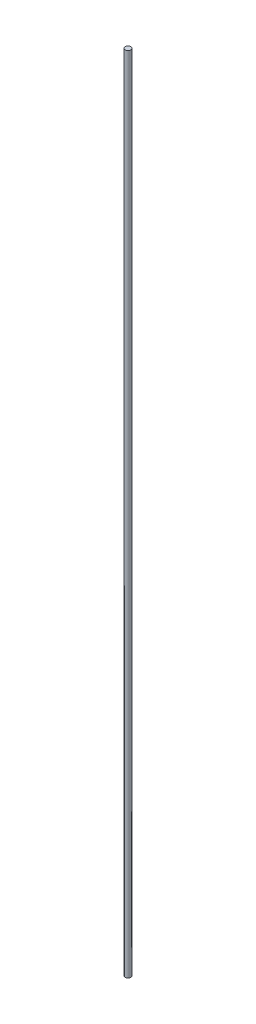
SolidWorks part; units mm, degrees
ref_plane "Front Plane" through (0, 0, 0) normal (0, 0, 1) x (1, 0, 0)
ref_plane "Top Plane" through (0, 0, 0) normal (0, 1, 0) x (1, 0, 0)
ref_plane "Right Plane" through (0, 0, 0) normal (1, 0, 0) x (0, 0, -1)
sketch "Sketch1" plane through (0, 0, 0) normal (0, 1, 0) x (1, 0, 0)
  circle A0 centre (0, 0) radius 1.5
  dimension "D1" = 3
extrude "Boss-Extrude1" add sketch "Sketch1" along normal blind 424
